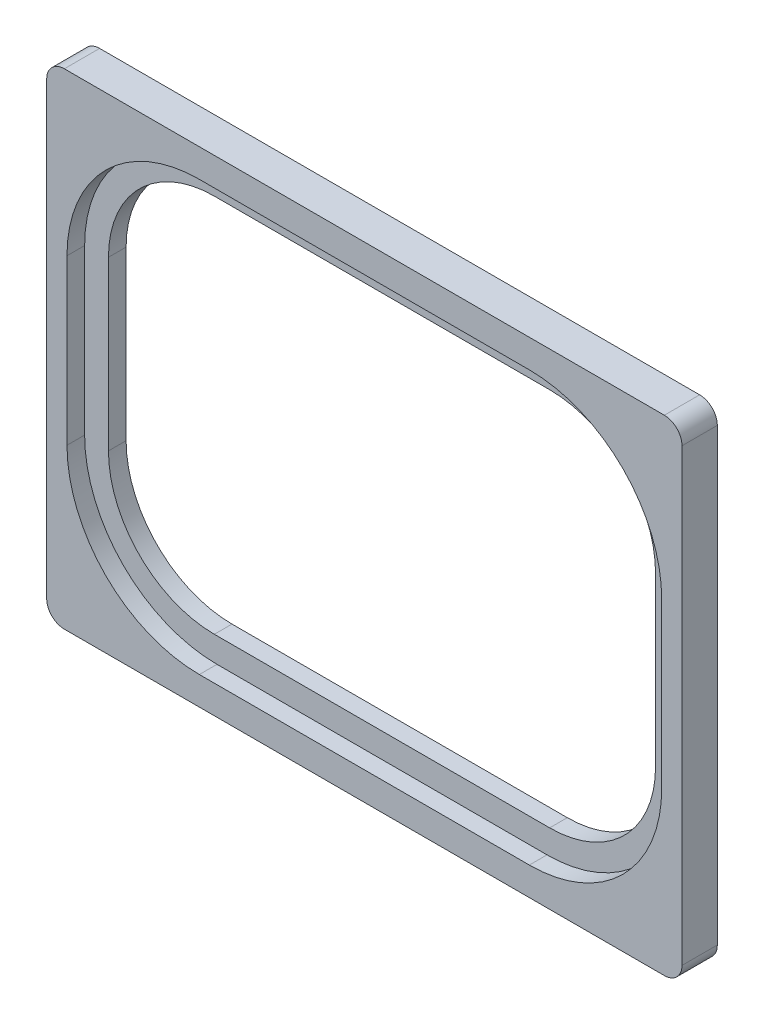
SolidWorks part; units mm, degrees
ref_plane "前视基准面" through (0, 0, 0) normal (0, 0, 1) x (1, 0, 0)
ref_plane "上视基准面" through (0, 0, 0) normal (0, 1, 0) x (1, 0, 0)
ref_plane "右视基准面" through (0, 0, 0) normal (1, 0, 0) x (0, 0, -1)
other "Configuration Table"
sketch "草图1" plane through (0, 0, 0) normal (0, 0, 1) x (1, 0, 0)
  line L1 (36, 27.5) -> (-36, 27.5)
  line L2 (36, 27.5) -> (36, -27.5)
  line L3 (36, -27.5) -> (-36, -27.5)
  line L4 (-36, 27.5) -> (-36, -27.5)
  line L5 (36, 27.5) -> (-36, -27.5) construction
  line L6 (36, -27.5) -> (-36, 27.5) construction
  point P0 (0, 0)
  dimension "D1" = 72
  dimension "D2" = 55
extrude "凸台-拉伸1" add sketch "草图1" along normal blind 4
fillet "圆角1" radius 2 4 edges at (-36, -27.5, 2) (36, -27.5, 2) (36, 27.5, 2) (-36, 27.5, 2)
sketch "草图2" plane through (0, 0, 4) normal (0, 0, 1) x (1, 0, 0)
  line L0 (-31, 9.5) -> (-31, -9.5)
  line L5 (31, 21.5) -> (-31, -21.5) construction
  line L6 (31, -21.5) -> (-31, 21.5) construction
  line L7 (-19, -21.5) -> (19, -21.5)
  line L8 (31, -9.5) -> (31, 9.5)
  line L9 (19, 21.5) -> (-19, 21.5)
  arc A4 (31, 9.5) -> (19, 21.5) centre (19, 9.5) ccw
  arc A5 (31, -9.5) -> (19, -21.5) centre (19, -9.5) cw
  arc A6 (-31, -9.5) -> (-19, -21.5) centre (-19, -9.5) ccw
  arc A7 (-31, 9.5) -> (-19, 21.5) centre (-19, 9.5) cw
  point P0 (0, 0)
  dimension "D3" = 43
  dimension "D1" = 12
  dimension "D2" = 62
extrude "切除-拉伸1" cut sketch "草图2" against normal up to next
sketch "草图3" plane through (0, 0, 4) normal (0, 0, 1) x (1, 0, 0)
  line L1 (18.7, 24.3) -> (-18.7, 24.3)
  line L2 (33.7, 9.3) -> (33.7, -9.3)
  line L3 (18.7, -24.3) -> (-18.7, -24.3)
  line L4 (-33.7, 9.3) -> (-33.7, -9.3)
  line L5 (33.7, 24.3) -> (-33.7, -24.3) construction
  line L6 (33.7, -24.3) -> (-33.7, 24.3) construction
  arc A0 (33.7, 9.3) -> (18.7, 24.3) centre (18.7, 9.3) ccw
  arc A1 (33.7, -9.3) -> (18.7, -24.3) centre (18.7, -9.3) cw
  arc A2 (-33.7, -9.3) -> (-18.7, -24.3) centre (-18.7, -9.3) ccw
  arc A3 (-33.7, 9.3) -> (-18.7, 24.3) centre (-18.7, 9.3) cw
  point P0 (0, 0)
  dimension "D1" = 15
  dimension "D2" = 67.4
  dimension "D3" = 48.6
extrude "切除-拉伸2" cut sketch "草图3" against normal blind 2
